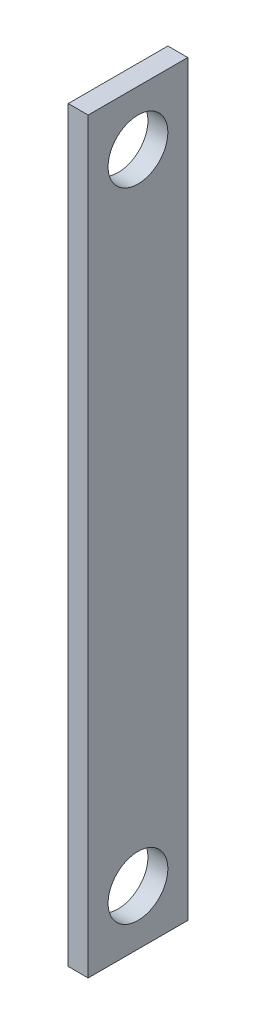
SolidWorks part; units mm, degrees
ref_plane "Front Plane" through (0, 0, 0) normal (0, 0, 1) x (1, 0, 0)
ref_plane "Top Plane" through (0, 0, 0) normal (0, 1, 0) x (1, 0, 0)
ref_plane "Right Plane" through (0, 0, 0) normal (1, 0, 0) x (0, 0, -1)
sketch "Sketch1" plane through (0, 0, 0) normal (1, 0, 0) x (0, 0, -1)
  line L1 (-5, -37.5) -> (5, -37.5)
  line L2 (-5, -37.5) -> (-5, 37.5)
  line L3 (-5, 37.5) -> (5, 37.5)
  line L4 (5, -37.5) -> (5, 37.5)
  line L5 (-5, -37.5) -> (5, 37.5) construction
  line L6 (-5, 37.5) -> (5, -37.5) construction
  point P0 (0, 0)
  dimension "D1" = 75
  dimension "D2" = 10
extrude "Boss-Extrude1" add sketch "Sketch1" along normal blind 2
sketch "Sketch2" plane through (2, 0, 0) normal (1, 0, 0) x (0, 0, -1)
  circle A0 centre (0, -32) radius 3
  circle A1 centre (0, 32) radius 3
  dimension "D3" = 6
  dimension "D4" = 6
  dimension "D1" = 32
  dimension "D2" = 32
extrude "Cut-Extrude1" cut sketch "Sketch2" against normal up to surface (2 mm away) up to face at (0, 0, 0)
